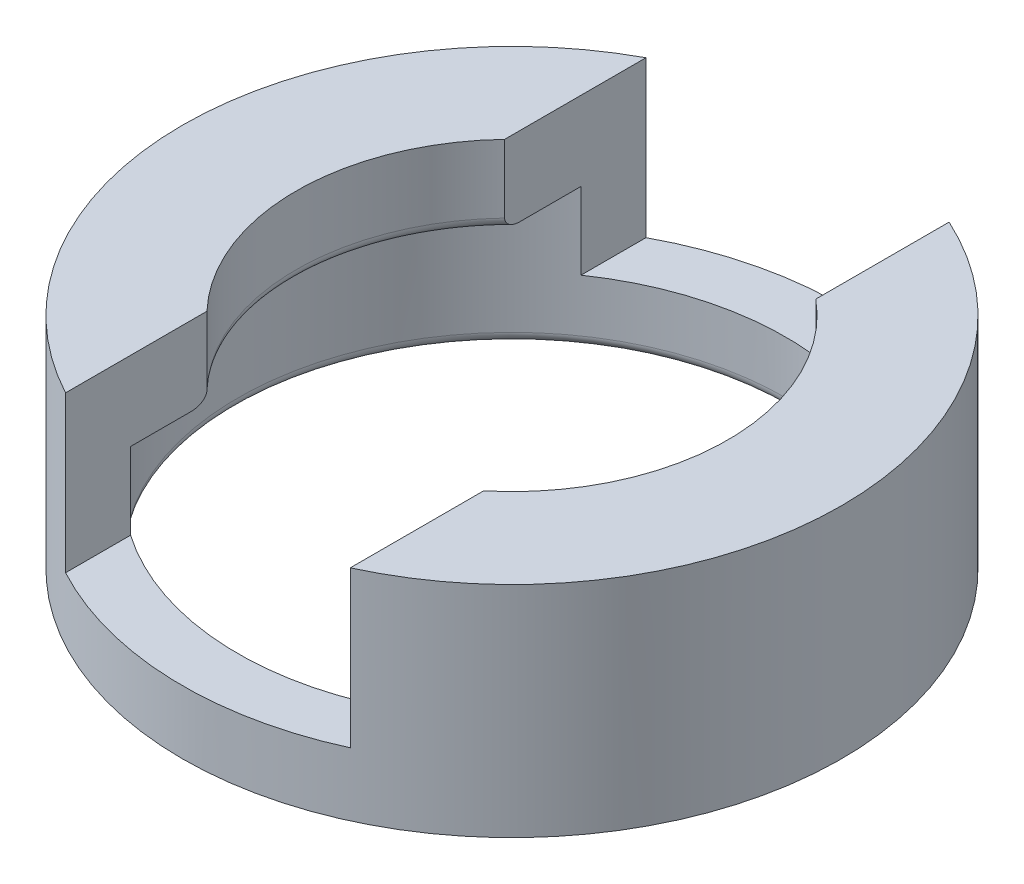
SolidWorks part; units mm, degrees
ref_plane "Front Plane" through (0, 0, 0) normal (0, 0, 1) x (1, 0, 0)
ref_plane "Top Plane" through (0, 0, 0) normal (0, 1, 0) x (1, 0, 0)
ref_plane "Right Plane" through (0, 0, 0) normal (1, 0, 0) x (0, 0, -1)
sketch "Sketch1" plane through (0, 0, 0) normal (0, 1, 0) x (1, 0, 0)
  circle A0 centre (0, 0) radius 30.55
extrude "Boss-Extrude1" add sketch "Sketch1" along normal blind 20.32
sketch "Sketch2" plane through (0, 0, 0) normal (0, -1, 0) x (1, 0, 0)
  circle A0 centre (0, 0) radius 25.404
extrude "Cut-Extrude1" cut sketch "Sketch2" against normal blind 13
sketch "Sketch3" plane through (0, 20.32, 0) normal (0, 1, 0) x (1, 0, 0)
  circle A0 centre (0, 0) radius 20
extrude "Cut-Extrude2" cut sketch "Sketch3" against normal through all
fillet "Fillet1" radius 1 1 edges at (0, 0, -25.404)
fillet "Fillet2" radius 1 1 edges at (0, 13, -20)
sketch "Sketch4" plane through (0, 0, 0) normal (0, 0, 1) x (1, 0, 0)
  line L1 (-14.4792, 30.1944) -> (12.7653, 30.1944)
  line L2 (-14.4792, 30.1944) -> (-14.4792, 5.8754)
  line L3 (-14.4792, 5.8754) -> (12.7653, 5.8754)
  line L4 (12.7653, 30.1944) -> (12.7653, 5.8754)
extrude "Cut-Extrude3" cut sketch "Sketch4" against normal through all both and the other way through all
